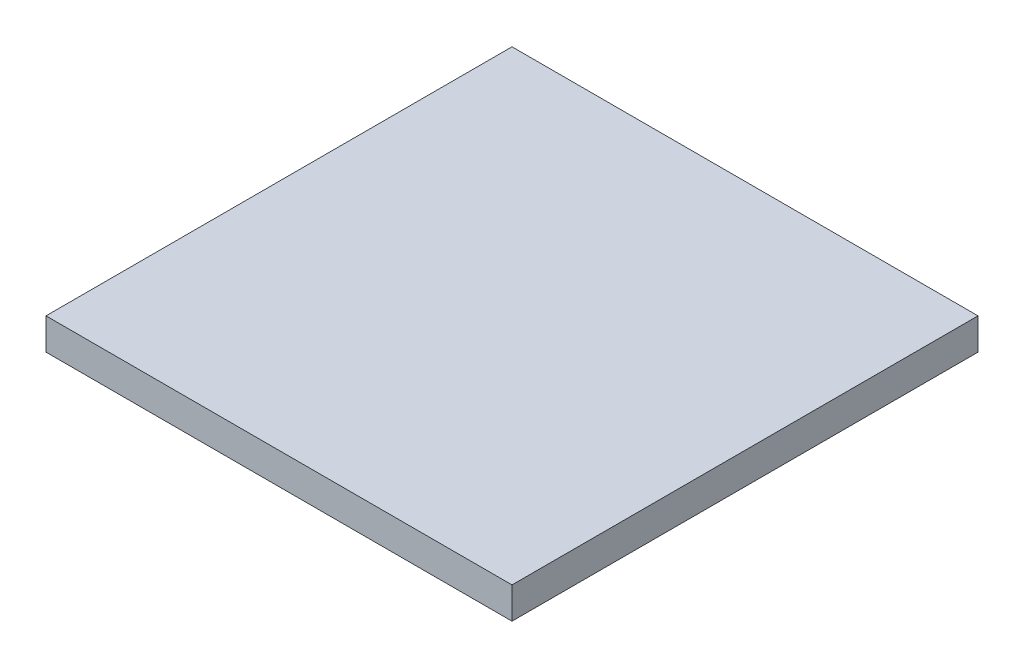
SolidWorks part; units mm, degrees
material "Silicon"
ref_plane "Front Plane" through (0, 0, 0) normal (0, 0, 1) x (1, 0, 0)
ref_plane "Top Plane" through (0, 0, 0) normal (0, 1, 0) x (1, 0, 0)
ref_plane "Right Plane" through (0, 0, 0) normal (1, 0, 0) x (0, 0, -1)
sketch "Sketch1" plane through (0, 0, 0) normal (0, 1, 0) x (1, 0, 0)
  line L0 (25.9, 29.225) -> (32.9, 29.225)
  line L1 (0, 0) -> (50.8, 0)
  line L2 (0, 0) -> (0, 44.45)
  line L3 (0, 44.45) -> (50.8, 44.45)
  line L4 (50.8, 0) -> (50.8, 44.45)
  line L5 (20.4, 27.225) -> (30.4, 27.225)
  line L6 (20.4, 27.225) -> (20.4, 17.225)
  line L7 (20.4, 17.225) -> (30.4, 17.225)
  line L8 (30.4, 27.225) -> (30.4, 17.225)
  line L9 (17.9, 15.225) -> (32.9, 15.225)
  line L10 (17.9, 15.225) -> (17.9, 29.225)
  line L11 (17.9, 29.225) -> (24.9, 29.225)
  line L12 (32.9, 15.225) -> (32.9, 29.225)
  line L14 (22.9, 44.45) -> (22.9, 39.45)
  line L15 (22.9, 39.45) -> (24.9, 39.45)
  line L16 (27.9, 44.45) -> (27.9, 39.45)
  line L18 (24.9, 39.45) -> (24.9, 29.225)
  line L20 (25.9, 39.45) -> (25.9, 29.225)
  line L21 (25.9, 39.45) -> (27.9, 39.45)
  line L22 (5, 38.4487) -> (0, 38.4487)
  line L31 (5, 25.4487) -> (5, 23.4487)
  line L32 (45.8, 35.4487) -> (45.8, 33.4487)
  line L49 (18.4, 27.725) -> (32.4, 27.725)
  line L50 (18.4, 27.725) -> (18.4, 28.725)
  line L51 (18.4, 28.725) -> (32.4, 28.725)
  line L52 (32.4, 27.725) -> (32.4, 28.725)
  line L53 (50.8, 38.4487) -> (45.8, 38.4487)
  line L55 (50.8, 33.4487) -> (45.8, 33.4487)
  line L56 (45.8, 38.4487) -> (45.8, 36.4487)
  line L57 (45.8, 36.4487) -> (33.9, 36.4487)
  line L59 (45.8, 35.4487) -> (34.9, 35.4487)
  line L62 (33.9, 36.4487) -> (33.9, 15.225)
  line L63 (33.9, 15.225) -> (34.9, 15.225)
  line L64 (34.9, 35.4487) -> (34.9, 15.225)
  line L65 (45.8, 15.225) -> (45.8, 13.225)
  line L67 (35.9, 15.225) -> (35.9, 29.225)
  line L68 (35.9, 29.225) -> (36.9, 29.225)
  line L69 (36.9, 16.225) -> (36.9, 29.225)
  line L70 (35.9, 15.225) -> (45.8, 15.225)
  line L72 (36.9, 16.225) -> (45.8, 16.225)
  line L74 (50.8, 18.225) -> (45.8, 18.225)
  line L76 (50.8, 13.225) -> (45.8, 13.225)
  line L77 (45.8, 18.225) -> (45.8, 16.225)
  line L78 (5, 35.4487) -> (5, 33.4487)
  line L81 (0, 33.4487) -> (5, 33.4487)
  line L82 (5, 38.4487) -> (5, 36.4487)
  line L83 (5, 36.4487) -> (16.9, 36.4487)
  line L85 (5, 35.4487) -> (15.9, 35.4487)
  line L88 (16.9, 36.4487) -> (16.9, 15.225)
  line L89 (16.9, 15.225) -> (15.9, 15.225)
  line L90 (15.9, 35.4487) -> (15.9, 15.225)
  line L91 (0, 28.4487) -> (5, 28.4487)
  line L93 (0, 23.4487) -> (5, 23.4487)
  line L94 (5, 28.4487) -> (5, 26.4487)
  line L103 (5, 26.4487) -> (13.9, 26.4487)
  line L105 (5, 25.4487) -> (13.9, 25.4487)
  line L107 (14.9, 29.225) -> (13.9, 29.225)
  line L108 (14.9, 29.225) -> (14.9, 23.4487)
  line L109 (14.9, 23.4487) -> (13.9, 23.4487)
  line L110 (13.9, 29.225) -> (13.9, 26.4487)
  line L111 (13.9, 22.9487) -> (14.9, 22.9487)
  line L112 (13.9, 22.9487) -> (13.9, 16.225)
  line L114 (14.9, 22.9487) -> (14.9, 15.225)
  line L119 (14.9, 15.225) -> (5, 15.225)
  line L121 (13.9, 16.225) -> (5, 16.225)
  line L123 (0, 18.225) -> (5, 18.225)
  line L125 (0, 13.225) -> (5, 13.225)
  line L126 (5, 18.225) -> (5, 16.225)
  line L127 (13.9, 25.4487) -> (13.9, 23.4487)
  line L128 (5, 15.225) -> (5, 13.225)
  line L130 (18.9, 5) -> (20.9, 5)
  line L131 (17.9, 14.725) -> (32.9, 14.725)
  line L133 (18.9, 13.725) -> (32.9, 13.725)
  line L134 (32.9, 14.725) -> (32.9, 13.725)
  line L136 (17.9, 14.725) -> (17.9, 5)
  line L138 (18.9, 13.725) -> (18.9, 5)
  line L140 (15.9, 0) -> (15.9, 5)
  line L141 (15.9, 5) -> (17.9, 5)
  line L142 (20.9, 0) -> (20.9, 5)
  line L143 (19.4, 13.225) -> (32.9, 13.225)
  line L144 (19.4, 13.225) -> (19.4, 12.225)
  line L145 (19.4, 12.225) -> (31.9, 12.225)
  line L148 (32.9, 13.225) -> (32.9, 5)
  line L150 (31.9, 12.225) -> (31.9, 5)
  line L152 (29.9, 0) -> (29.9, 5)
  line L153 (29.9, 5) -> (31.9, 5)
  line L154 (34.9, 0) -> (34.9, 5)
  line L155 (32.9, 5) -> (34.9, 5)
  circle A0 centre (9.7727, 40.45) radius 2.0013
  circle A1 centre (41.5129, 40.45) radius 2
  point P13 (32.9, 22.225)
  point P22 (27.9, 41.95)
  point P77 (14.4, 23.4487)
  dimension "D17" = 4
  dimension "D19" = 4
  dimension "D20" = 4.0026
  dimension "D1" = 50.8
  dimension "D2" = 44.45
  dimension "D3" = 10
  dimension "D4" = 10
  dimension "D5" = 20.4
  dimension "D6" = 17.225
  dimension "D7" = 2.5
  dimension "D8" = 2.5
  dimension "D9" = 2
  dimension "D10" = 2
  dimension "D11" = 5
  dimension "D12" = 5
  dimension "D13" = 2
  dimension "D14" = 22.9
  dimension "D15" = 2
  dimension "D16" = 14
  dimension "D18" = 4
  dimension "D21" = 0.5
  dimension "D22" = 1
  dimension "D23" = 5
  dimension "D24" = 5
  dimension "D25" = 5
  dimension "D26" = 5
  dimension "D27" = 2
  dimension "D28" = 1
  dimension "D29" = 1
  dimension "D30" = 1
  dimension "D31" = 1
  dimension "D32" = 2
  dimension "D33" = 2
  dimension "D34" = 5
  dimension "D35" = 5
  dimension "D36" = 5
  dimension "D37" = 5
  dimension "D38" = 2
  dimension "D39" = 2
  dimension "D40" = 1
  dimension "D41" = 1
  dimension "D42" = 2
  dimension "D43" = 1
  dimension "D44" = 1
  dimension "D45" = 0.5
  dimension "D46" = 10.225
  dimension "D47" = 0.5
  dimension "D48" = 2
  dimension "D49" = 2
  dimension "D50" = 2
  dimension "D51" = 0
  dimension "D52" = 1
  dimension "D53" = 1
  dimension "D54" = 0.5
  dimension "D55" = 1
  dimension "D56" = 2
  dimension "D57" = 5
  dimension "D58" = 2
  dimension "D59" = 2
  dimension "D60" = 1
  dimension "D61" = 5
  dimension "D62" = 0.5
  dimension "D63" = 0.5
  dimension "D64" = 1
  dimension "D66" = 1
  dimension "D67" = 2
  dimension "D68" = 2
  dimension "D69" = 5
sketch "Sketch2" plane through (0, 0, 0) normal (0, 1, 0) x (1, 0, 0)
  line L1 (20.4, 27.225) -> (30.4, 27.225)
  line L2 (20.4, 27.225) -> (20.4, 17.225)
  line L3 (20.4, 17.225) -> (30.4, 17.225)
  line L4 (30.4, 27.225) -> (30.4, 17.225)
extrude "Boss-Extrude1" add sketch "Sketch2" along normal blind 0.675
